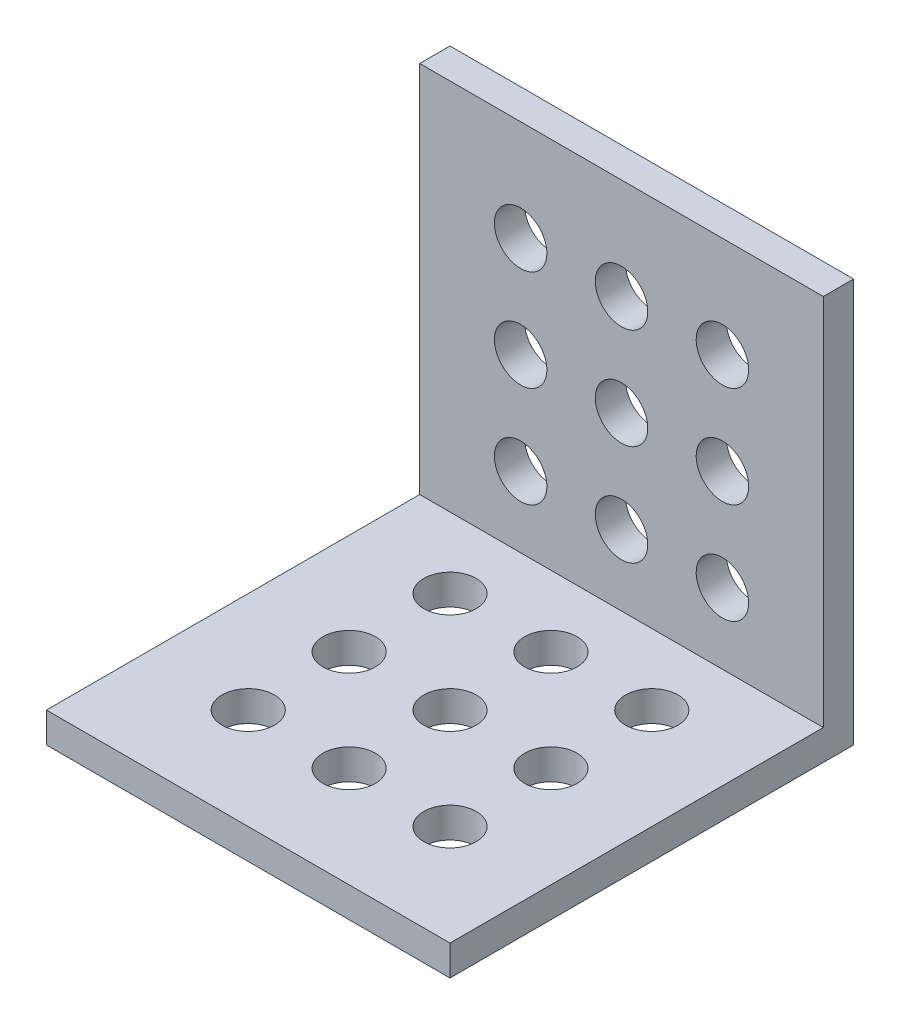
SolidWorks part; units mm, degrees
ref_plane "Front Plane" through (0, 0, 0) normal (0, 0, 1) x (1, 0, 0)
ref_plane "Top Plane" through (0, 0, 0) normal (0, 1, 0) x (1, 0, 0)
ref_plane "Right Plane" through (0, 0, 0) normal (1, 0, 0) x (0, 0, -1)
sketch "Sketch1" plane through (0, 0, 0) normal (1, 0, 0) x (0, 0, -1)
  line L0 (0, 0) -> (0, 3)
  line L1 (0, 3) -> (37, 3)
  line L2 (37, 3) -> (37, 40)
  line L3 (37, 40) -> (40, 40)
  line L4 (40, 40) -> (40, 0)
  line L5 (40, 0) -> (0, 0)
  dimension "D1" = 3
  dimension "D2" = 40
extrude "Boss-Extrude1" add sketch "Sketch1" against normal blind 40
sketch "Sketch2" plane through (0, 3, 0) normal (0, 1, 0) x (1, 0, 0)
  line L0 (-40, 37) -> (-40, 0) construction
  line L3 (-40, 0) -> (0, 0) construction
  circle A11 centre (-30, 10) radius 2.6
  circle A12 centre (-20, 10) radius 2.6
  circle A13 centre (-10, 10) radius 2.6
  circle A14 centre (-20, 20) radius 2.6
  circle A15 centre (-10, 20) radius 2.6
  circle A16 centre (-20, 30) radius 2.6
  circle A17 centre (-10, 30) radius 2.6
  circle A18 centre (-30, 20) radius 2.6
  circle A19 centre (-30, 30) radius 2.6
  dimension "D2" = 10
  dimension "D7" = 10
  dimension "D3" = 5.2
  dimension "D1" = 10
  dimension "D5" = 3
  dimension "D6" = 10
  dimension "D4" = 3
extrude "Cut-Extrude1" cut sketch "Sketch2" against normal through all
sketch "Sketch3" plane through (0, 0, 0) normal (1, 0, 0) x (0, 0, -1)
  line L0 (37, 3) -> (40, 0) construction
sketch "Sketch4" plane through (-40, 0, 0) normal (-1, 0, 0) x (0, 0, 1)
  line L0 (-40, 0) -> (-37, 3) construction
ref_plane "Plane1" through (0, 20, -20) normal (0, 0.7071, -0.7071) x (1, 0, 0)
mirror "Mirror1" about plane through (0, 20, -20) normal (0, 0.7071, -0.7071) of "Cut-Extrude1"
